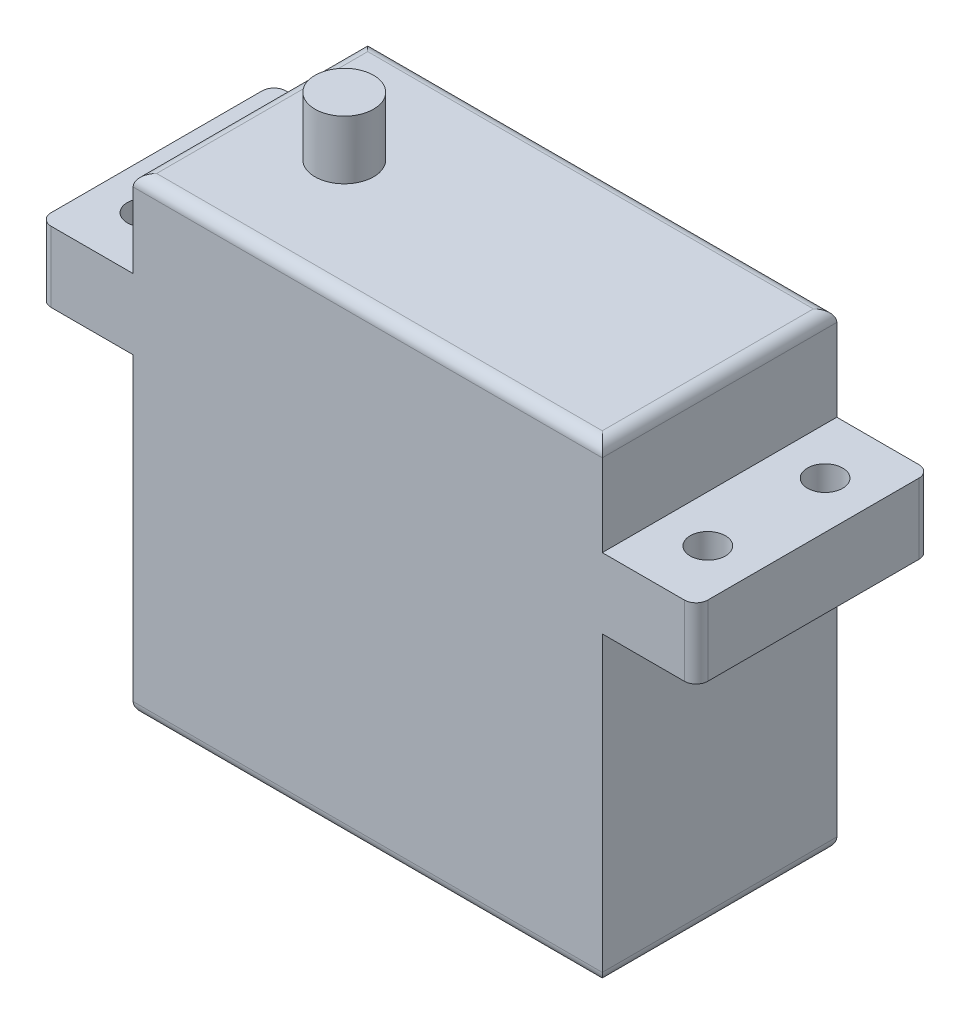
SolidWorks part; units mm, degrees
ref_plane "Ön Düzlem" through (0, 0, 0) normal (0, 0, 1) x (1, 0, 0)
ref_plane "Üst Düzlem" through (0, 0, 0) normal (0, 1, 0) x (1, 0, 0)
ref_plane "Sağ Düzlem" through (0, 0, 0) normal (1, 0, 0) x (0, 0, -1)
sketch "Çizim1" plane through (0, 0, 0) normal (0, 0, 1) x (1, 0, 0)
  line L1 (-20, 20) -> (20, 20)
  line L2 (-20, 20) -> (-20, -20)
  line L3 (-20, -20) -> (20, -20)
  line L4 (20, 20) -> (20, -20)
  line L5 (-20, 20) -> (20, -20) construction
  line L6 (-20, -20) -> (20, 20) construction
  point P0 (0, 0)
  dimension "D1" = 40
  dimension "D2" = 40
extrude "Yükseklik-Ekstrüzyon1" add sketch "Çizim1" along normal blind 20
sketch "Çizim2" plane through (20, 0, 0) normal (1, 0, 0) x (0, 0, -1)
  line L0 (-20, 6) -> (0, 6)
  line L1 (-20, -20) -> (-20, 20) construction
  line L2 (0, -20) -> (0, 20) construction
  line L3 (-20, 12) -> (0, 12)
  line L4 (-20, -20) -> (0, -20) construction
  line L6 (-20, 12) -> (-20, 6)
  line L7 (0, 12) -> (0, 6)
  dimension "D1" = 26
  dimension "D2" = 6
extrude "Yükseklik-Ekstrüzyon2" add sketch "Çizim2" along normal blind 8
sketch "Çizim3" plane through (-20, 0, 0) normal (-1, 0, 0) x (0, 0, 1)
  line L0 (0, 6.6042) -> (20, 6.6042)
  line L1 (0, 20) -> (0, -20) construction
  line L2 (20, 20) -> (20, -20) construction
  line L3 (20, -20) -> (0, -20) construction
  line L4 (0, 12.6042) -> (20, 12.6042)
  line L5 (0, 12.6042) -> (0, 6.6042)
  line L6 (20, 12.6042) -> (20, 6.6042)
  dimension "D1" = 26.6042
  dimension "D2" = 6
extrude "Yükseklik-Ekstrüzyon3" add sketch "Çizim3" along normal blind 8
sketch "Çizim4" plane through (0, 20, 0) normal (0, 1, 0) x (1, 0, 0)
  line L0 (-28, -10) -> (28, -10) construction
  line L1 (-28, -20) -> (-28, 0) construction
  line L2 (28, 0) -> (28, -20) construction
  circle A0 centre (-12, -10) radius 2.5
  dimension "D1" = 5
  dimension "D2" = 16
extrude "Yükseklik-Ekstrüzyon4" add sketch "Çizim4" along normal blind 5
sketch "Çizim5" plane through (0, 12.6042, 0) normal (0, 1, 0) x (1, 0, 0)
  line L0 (-28, -10) -> (28, -10) construction
  line L1 (-28, -20) -> (-28, 0) construction
  line L2 (28, 0) -> (28, -20) construction
  line L3 (0, 0) -> (0, -20) construction
  line L4 (20, -20) -> (-20, -20) construction
  line L5 (-24, 0) -> (-24, -20) construction
  line L6 (-28, 0) -> (-20, 0) construction
  line L7 (-28, -20) -> (-20, -20) construction
  circle A0 centre (-24, -5) radius 1.5
  circle A1 centre (-24, -15) radius 1.5
  circle A2 centre (24, -15) radius 1.5
  circle A3 centre (24, -5) radius 1.5
  dimension "D3" = 3
  dimension "D1" = 5
  dimension "D2" = 5
extrude "Kes-Ekstrüzyon1" cut sketch "Çizim5" against normal blind 15
fillet "Radyus1" radius 1 4 edges at (20, 20, 10) (-20, 20, 10) (0, 20, 0) (0, 20, 20)
fillet "Radyus2" radius 1 4 edges at (-20, -20, 10) (0, -20, 20) (20, -20, 10) (0, -20, 0)
fillet "Radyus3" radius 1 1 edges at (28, 9, 20)
fillet "Radyus4" radius 1 1 edges at (-28, 9.6042, 0)
fillet "Radyus5" radius 1 2 edges at (28, 9, 0) (-28, 9.6042, 20)
